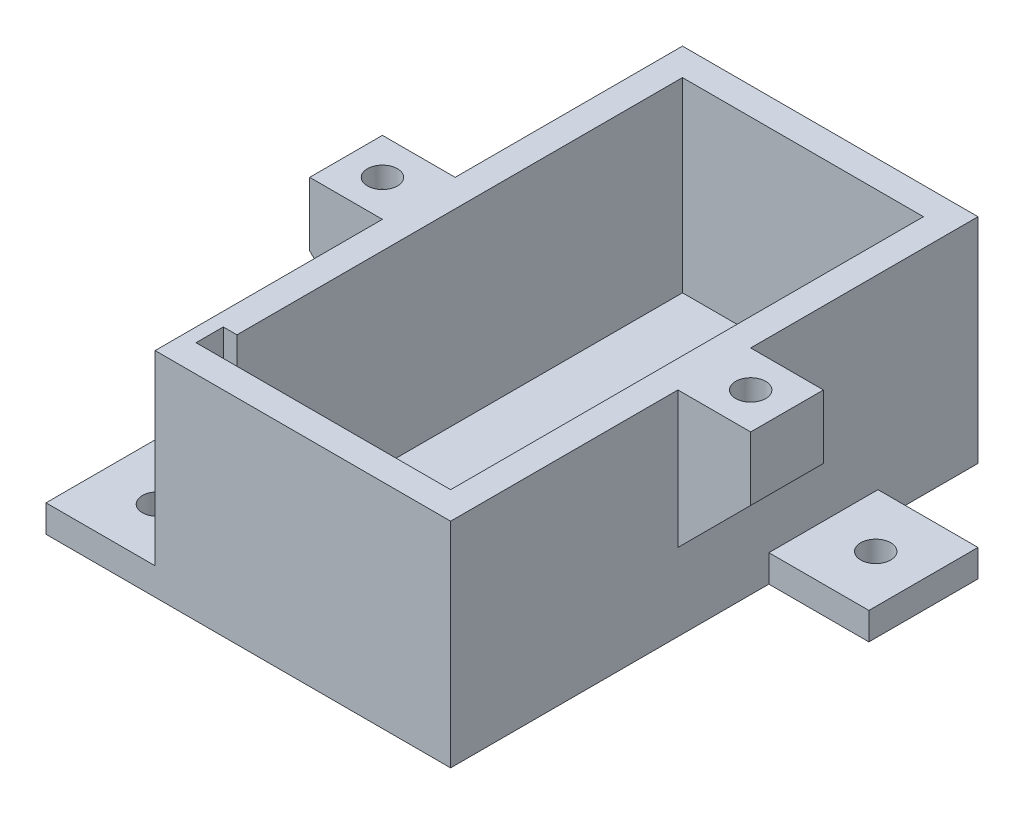
SolidWorks part; units mm, degrees
ref_plane "Front Plane" through (0, 0, 0) normal (0, 0, 1) x (1, 0, 0)
ref_plane "Top Plane" through (0, 0, 0) normal (0, 1, 0) x (1, 0, 0)
ref_plane "Right Plane" through (0, 0, 0) normal (1, 0, 0) x (0, 0, -1)
sketch "Sketch1" plane through (0, 0, 0) normal (0, 0, 1) x (1, 0, 0)
  line L0 (3, 20.5) -> (3, 23.5)
  line L1 (0, 0) -> (32.5, 0)
  line L2 (0, 0) -> (0, 23.5)
  line L4 (32.5, 0) -> (32.5, 23.5)
  line L5 (3, 3) -> (29.5, 3)
  line L6 (3, 3) -> (3, 20.5)
  line L8 (29.5, 3) -> (29.5, 20.5)
  line L9 (29.5, 20.5) -> (29.5, 23.5)
  line L10 (0, 23.5) -> (3, 23.5)
  line L11 (29.5, 23.5) -> (32.5, 23.5)
  dimension "D1" = 3
  dimension "D2" = 3
  dimension "D3" = 17.5
  dimension "D4" = 26.5
  dimension "D5" = 3
extrude "Boss-Extrude1" add sketch "Sketch1" along normal blind 52
sketch "Sketch2" plane through (0, 0, 0) normal (0, 0, -1) x (-1, 0, 0)
  line L1 (-32.5, 0) -> (0, 0)
  line L2 (-32.5, 0) -> (-32.5, 23.5)
  line L3 (-32.5, 23.5) -> (0, 23.5)
  line L4 (0, 0) -> (0, 23.5)
extrude "Boss-Extrude2" add sketch "Sketch2" along normal blind 3
sketch "Sketch3" plane through (0, 23.5, 0) normal (0, 1, 0) x (1, 0, 0)
  line L0 (0, -52) -> (0, 3) construction
  line L1 (0, -30) -> (-8, -30)
  line L2 (0, -30) -> (0, -22)
  line L3 (0, -22) -> (-8, -22)
  line L4 (-8, -30) -> (-8, -22)
  line L5 (32.5, -52) -> (32.5, 3) construction
  line L6 (32.5, -30) -> (40.5, -30)
  line L7 (32.5, -30) -> (32.5, -22)
  line L8 (32.5, -22) -> (40.5, -22)
  line L9 (40.5, -30) -> (40.5, -22)
  line L11 (3, -52) -> (3, 0) construction
  circle A0 centre (-4, -26) radius 1.65
  circle A1 centre (36.5, -26) radius 1.65
  point P12 (0, -26)
  point P18 (-4, -30)
  point P19 (-8, -26)
  point P20 (36.5, -30)
  point P21 (40.5, -26)
  point P24 (3, -26)
  dimension "D4" = 3.3
  dimension "D1" = 8
  dimension "D2" = 0
  dimension "D3" = 8
extrude "Boss-Extrude3" add sketch "Sketch3" against normal blind 15
sketch "Sketch4" plane through (0, 23.5, 0) normal (0, 1, 0) x (1, 0, 0)
  line L1 (-1.0671, -27.3607) -> (-1.3552, -24.1404)
  line L2 (-1.3552, -24.1404) -> (-4.2881, -22.7797)
  line L3 (-4.2881, -22.7797) -> (-6.9329, -24.6393)
  line L4 (-6.9329, -24.6393) -> (-6.6448, -27.8596)
  line L5 (-6.6448, -27.8596) -> (-3.7119, -29.2203)
  line L6 (-3.7119, -29.2203) -> (-1.0671, -27.3607)
  line L7 (39.4329, -27.3607) -> (39.1448, -24.1404)
  line L8 (39.1448, -24.1404) -> (36.2119, -22.7797)
  line L9 (36.2119, -22.7797) -> (33.5671, -24.6393)
  line L10 (33.5671, -24.6393) -> (33.8552, -27.8596)
  line L11 (33.8552, -27.8596) -> (36.7881, -29.2203)
  line L12 (36.7881, -29.2203) -> (39.4329, -27.3607)
  circle A0 centre (-4, -26) radius 2.8 construction
  circle A1 centre (36.5, -26) radius 2.8 construction
  dimension "D1" = 5.6
extrude "Cut-Extrude1" cut sketch "Sketch4" against normal blind 2.4 from offset 2.3 offset against normal yes
sketch "Sketch5" plane through (0, 0, 30) normal (0, 0, 1) x (1, 0, 0)
  line L13 (40.5, 8.5) -> (32.5, 8.5)
  line L14 (32.5, 8.5) -> (40.5, 16.5)
  line L15 (40.5, 8.5) -> (40.5, 23.5) construction
  line L16 (40.5, 16.5) -> (40.5, 8.5)
  line L17 (-8, 8.5) -> (0, 8.5)
  line L18 (0, 8.5) -> (-8, 16.5)
  line L19 (-8, 8.5) -> (-8, 23.5) construction
  line L20 (-8, 16.5) -> (-8, 8.5)
  dimension "D1" = 45
  dimension "D2" = 45
extrude "Cut-Extrude2" cut sketch "Sketch5" against normal through all
sketch "Sketch6" plane through (0, 0, 52) normal (0, 0, 1) x (1, 0, 0)
  line L1 (0, 0) -> (32.5, 0)
  line L2 (0, 0) -> (0, 23.5)
  line L3 (0, 23.5) -> (32.5, 23.5)
  line L4 (32.5, 0) -> (32.5, 23.5)
extrude "Boss-Extrude5" add sketch "Sketch6" along normal blind 3
sketch "Sketch7" plane through (0, 3, 0) normal (0, 1, 0) x (1, 0, 0)
  line L0 (29.5, -52) -> (3, -52) construction
  line L1 (3, -52) -> (13, -52)
  line L2 (3, -52) -> (3, -42)
  line L3 (3, -42) -> (13, -42)
  line L4 (13, -52) -> (13, -42)
  line L5 (3, -52) -> (3, 0) construction
  dimension "D1" = 10
  dimension "D2" = 10
  dimension "D3" = 0
extrude "Cut-Extrude3" cut sketch "Sketch7" against normal blind 3
sketch "Sketch8" plane through (0, 23.5, 0) normal (0, 1, 0) x (1, 0, 0)
  line L0 (3, -42) -> (3, 0) construction
  line L1 (11.25, -52) -> (1.5, -52)
  line L2 (11.25, -52) -> (11.25, -49)
  line L3 (11.25, -49) -> (1.5, -49)
  line L4 (1.5, -52) -> (1.5, -49)
  point P7 (0, 0)
  dimension "D1" = 1.5
  dimension "D2" = 3
extrude "Cut-Extrude4" cut sketch "Sketch8" against normal blind 22
sketch "Sketch9" plane through (0, 0, 0) normal (0, -1, 0) x (1, 0, 0)
  line L0 (0, 55) -> (32.5, 55) construction
  line L10 (-5.75, 49) -> (0, 49) construction
  line L11 (0, 55) -> (0, -3) construction
  line L12 (38.25, 14) -> (32.5, 14) construction
  line L13 (32.5, 55) -> (32.5, -3) construction
  line L14 (32.5, 8) -> (43.5, 8)
  line L15 (43.5, 8) -> (43.5, 20)
  line L16 (43.5, 20) -> (32.5, 20)
  line L17 (0, 43) -> (-12, 43)
  line L18 (-12, 43) -> (-12, 55)
  line L19 (-12, 55) -> (0, 55)
  circle A0 centre (-5.75, 49) radius 1.65
  circle A1 centre (38.25, 14) radius 1.65
  point P18 (0, 0)
  point P19 (-12, 49)
  point P20 (0, 0)
  point P21 (0, 0)
  point P22 (43.5, 14)
  line M15 (0, 55) -> (0, -3)
  line M17 (32.5, -3) -> (32.5, 55)
  dimension "D1" = 3.3
  dimension "D2" = 44
  dimension "D3" = 35
  dimension "D4" = 12
  dimension "D5" = 12
  dimension "D6" = 11
  dimension "D7" = 12
  dimension "D8" = 0
extrude "Boss-Extrude6" add sketch "Sketch9" against normal blind 3 contours L15 L16 L14 A1 M17 | L19 L18 L17 A0 M15
